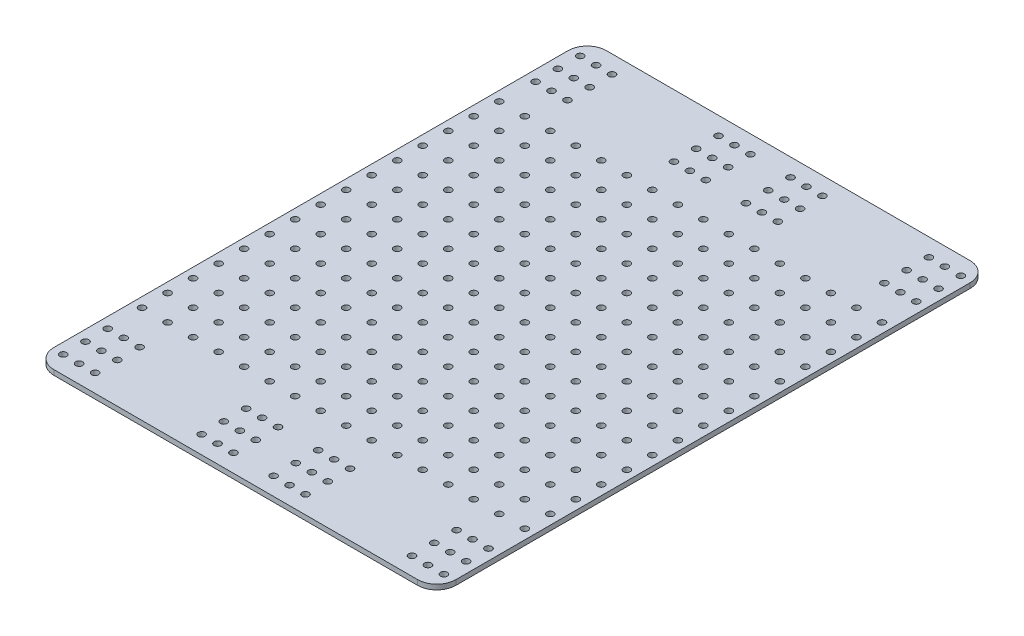
SolidWorks part; units mm, degrees
ref_plane "Front Plane" through (0, 0, 0) normal (0, 0, 1) x (1, 0, 0)
ref_plane "Top Plane" through (0, 0, 0) normal (0, 1, 0) x (1, 0, 0)
ref_plane "Right Plane" through (0, 0, 0) normal (1, 0, 0) x (0, 0, -1)
sketch "Sketch2" plane through (0, 50, 0) normal (0, 1, 0) x (1, 0, 0)
  line L6 (100.0588, 137.5) -> (-100.0588, 137.5)
  line L7 (100.0588, 137.5) -> (100.0588, -137.5)
  line L8 (100.0588, -137.5) -> (-100.0588, -137.5)
  line L9 (-100.0588, 137.5) -> (-100.0588, -137.5)
  line L10 (100.0588, 137.5) -> (-100.0588, -137.5) construction
  line L11 (100.0588, -137.5) -> (-100.0588, 137.5) construction
  point P0 (0, 0)
extrude "Boss-Extrude1" add sketch "Sketch2" along normal blind 2.5
sketch "Sketch4" plane through (0, 52.5, 0) normal (0, 1, 0) x (1, 0, 0)
  circle A0 centre (-9.9812, -128.65) radius 1.27 construction
  circle A1 centre (-9.9812, -106.4725) radius 1.27 construction
  circle A2 centre (-9.9812, -117.5612) radius 1.27 construction
  circle A3 centre (-17.9187, -117.5612) radius 1.27 construction
  circle A4 centre (-17.9187, -106.4725) radius 1.27 construction
  circle A5 centre (-25.8562, -106.4725) radius 1.27 construction
  circle A6 centre (-25.8562, -117.5612) radius 1.27 construction
  circle A7 centre (-17.9187, -128.65) radius 1.27 construction
  circle A8 centre (-25.8562, -128.65) radius 1.27 construction
  circle A9 centre (-86.8122, -117.5612) radius 1.27 construction
  circle A10 centre (-86.8122, -128.65) radius 1.27 construction
  circle A11 centre (-78.8747, -128.65) radius 1.27 construction
  circle A12 centre (-78.8747, -117.5612) radius 1.27 construction
  circle A13 centre (-78.8747, -106.4725) radius 1.27 construction
  circle A14 centre (-86.8122, -106.4725) radius 1.27 construction
  circle A15 centre (-94.7497, -106.4725) radius 1.27 construction
  circle A16 centre (-94.7497, -117.5612) radius 1.27 construction
  circle A17 centre (-94.7497, -128.65) radius 1.27 construction
  circle A18 centre (-9.9812, -128.65) radius 1.27 construction
  circle A19 centre (-9.9812, -106.4725) radius 1.27 construction
  circle A20 centre (-9.9812, -117.5612) radius 1.27 construction
  circle A21 centre (-17.9187, -117.5612) radius 1.27 construction
  circle A22 centre (-17.9187, -106.4725) radius 1.27 construction
  circle A23 centre (-25.8562, -106.4725) radius 1.27 construction
  circle A24 centre (-25.8562, -117.5612) radius 1.27 construction
  circle A25 centre (-17.9187, -128.65) radius 1.27 construction
  circle A26 centre (-25.8562, -128.65) radius 1.27 construction
  circle A27 centre (-86.8122, -117.5612) radius 1.27 construction
  circle A28 centre (-86.8122, -128.65) radius 1.27 construction
  circle A29 centre (-78.8747, -128.65) radius 1.27 construction
  circle A30 centre (-78.8747, -117.5612) radius 1.27 construction
  circle A31 centre (-78.8747, -106.4725) radius 1.27 construction
  circle A32 centre (-86.8122, -106.4725) radius 1.27 construction
  circle A33 centre (-94.7497, -106.4725) radius 1.27 construction
  circle A34 centre (-94.7497, -117.5612) radius 1.27 construction
  circle A35 centre (-94.7497, -128.65) radius 1.27 construction
hole_wizard "M3 Clearance Hole1" positions "3DSketch2" profile "Sketch6" hole size "M3" standard "ANSI Metric" end condition through all
sketch3d "3DSketch2"
  point P0 (-94.7497, 52.5, 106.4725)
  point P3 (-86.8122, 52.5, 106.4725)
  point P6 (-78.8747, 52.5, 106.4725)
  point P9 (-78.8747, 52.5, 117.5612)
  point P12 (-86.8122, 52.5, 117.5612)
  point P15 (-94.7497, 52.5, 117.5612)
  point P18 (-94.7497, 52.5, 128.65)
  point P21 (-86.8122, 52.5, 128.65)
  point P24 (-78.8747, 52.5, 128.65)
  point P27 (-25.8562, 52.5, 106.4725)
  point P30 (-17.9187, 52.5, 106.4725)
  point P33 (-9.9812, 52.5, 106.4725)
  point P35 (-9.9812, 52.5, 117.5612)
  point P38 (-17.9187, 52.5, 117.5612)
  point P41 (-25.8562, 52.5, 117.5612)
  point P44 (-25.8562, 52.5, 128.65)
  point P47 (-17.9187, 52.5, 128.65)
  point P50 (-9.9812, 52.5, 128.65)
  point P54 (-9.9812, 52.5, 106.4725)
sketch "Sketch6" plane through (-94.7497, 52.5, 106.4725) normal (1, 0, 0) x (0, 0, 1)
  line L0 (0, 0) -> (0, 2.5)
  line L1 (0, 2.5) -> (1.7, 2.5)
  line L2 (1.7, 2.5) -> (1.7, 0)
  line L5 (1.7, 0) -> (0, 0)
  line L11 (0, -6.35) -> (0, 107.95) construction
  dimension "Thru Hole Dia." = 3.4
  dimension "Thru Hole Depth" = 2.5
mirror "Mirror1" about plane through (0, 0, 0) normal (1, 0, 0) of "M3 Clearance Hole1"
mirror "Mirror2" about plane through (0, 0, 0) normal (0, 0, 1) of "M3 Clearance Hole1", "Mirror1"
fillet "Fillet1" radius 9.525 4 edges at (-100.0588, 51.25, -137.5) (100.0588, 51.25, 137.5) (-100.0588, 51.25, 137.5) (100.0588, 51.25, -137.5)
sketch "Sketch7" plane through (0, 52.5, 0) normal (0, 1, 0) x (1, 0, 0)
  line L1 (0, 0) -> (6.35, 0) construction
  line L2 (0, 0) -> (0, -6.35) construction
  line L3 (0, -6.35) -> (6.35, -6.35) construction
  line L4 (6.35, 0) -> (6.35, -6.35) construction
  point P6 (6.35, -6.35)
  dimension "D1" = 6.35
hole_wizard "M3 Clearance Hole2" positions "Sketch9" profile "Sketch10" hole size "M3" standard "ANSI Metric" end condition through all
sketch "Sketch9" plane through (0, 52.5, 0) normal (0, 1, 0) x (1, 0, 0)
  point P0 (6.35, 0)
  point P5 (6.35, -6.35)
  point P6 (0, 0)
  point P7 (6.35, 0)
sketch "Sketch10" plane through (6.35, 52.5, 0) normal (1, 0, 0) x (0, 0, 1)
  line L0 (0, 0) -> (0, 2.5)
  line L1 (0, 2.5) -> (1.7, 2.5)
  line L2 (1.7, 2.5) -> (1.7, 0)
  line L5 (1.7, 0) -> (0, 0)
  line L11 (0, -6.35) -> (0, 107.95) construction
  dimension "Thru Hole Dia." = 3.4
  dimension "Thru Hole Depth" = 2.5
pattern_linear "LPattern1" count 8 spacing 12.7 along (0, 0, 1) count 8 spacing 12.7 along (1, 0, 0) of "M3 Clearance Hole2"
mirror "Mirror3" about plane through (0, 0, 0) normal (0, 0, 1) of "LPattern1", "M3 Clearance Hole2"
mirror "Mirror4" about plane through (0, 0, 0) normal (1, 0, 0) of "Mirror3", "LPattern1", "M3 Clearance Hole2"
